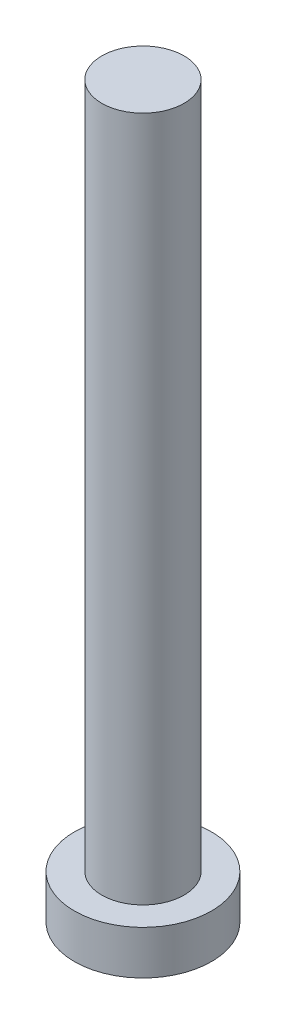
SolidWorks part; units mm, degrees
ref_plane "前视基准面" through (0, 0, 0) normal (0, 0, 1) x (1, 0, 0)
ref_plane "上视基准面" through (0, 0, 0) normal (0, 1, 0) x (1, 0, 0)
ref_plane "右视基准面" through (0, 0, 0) normal (1, 0, 0) x (0, 0, -1)
sketch "草图1" plane through (0, 0, 0) normal (0, 1, 0) x (1, 0, 0)
  circle A0 centre (0, 0) radius 2.5
extrude "凸台-拉伸1" add sketch "草图1" along normal blind 1.6
sketch "草图2" plane through (0, 1.6, 0) normal (0, 1, 0) x (1, 0, 0)
  circle A0 centre (0, 0) radius 1.5
extrude "凸台-拉伸2" add sketch "草图2" along normal blind 25
sketch "草图3" plane through (0, 0, 0) normal (0, -1, 0) x (1, 0, 0)
  line L0 (-0.5, 1) -> (-0.5, 1.75)
  line L1 (-1.75, -0.5) -> (-1, -0.5)
  line L2 (-1.75, -0.5) -> (-1.75, 0.5)
  line L3 (-1.75, 0.5) -> (-1, 0.5)
  line L4 (1.75, -0.5) -> (1.75, 0.5)
  line L5 (-1.75, -0.5) -> (1.75, 0.5) construction
  line L6 (-1.75, 0.5) -> (1.75, -0.5) construction
  line L7 (-0.5, -1.75) -> (0.5, -1.75)
  line L8 (-0.5, -1.75) -> (-0.5, -1)
  line L9 (-0.5, 1.75) -> (0.5, 1.75)
  line L10 (0.5, -1.75) -> (0.5, -1)
  line L11 (-0.5, -1.75) -> (0.5, 1.75) construction
  line L12 (-0.5, 1.75) -> (0.5, -1.75) construction
  line L13 (1, -0.5) -> (1.75, -0.5)
  line L14 (0.5, 1) -> (0.5, 1.75)
  line L15 (1, 0.5) -> (1.75, 0.5)
  arc A0 (1, -0.5) -> (0.5, -1) centre (1, -1) ccw
  arc A1 (-0.5, -1) -> (-1, -0.5) centre (-1, -1) ccw
  arc A2 (0.5, 1) -> (1, 0.5) centre (1, 1) ccw
  arc A3 (-0.5, 1) -> (-1, 0.5) centre (-1, 1) cw
  point P0 (0, 0)
  point P6 (0, 0)
  point P21 (0.5, 0.5)
  dimension "D1" = 0.5
extrude "切除-拉伸1" cut sketch "草图3" against normal blind 1
